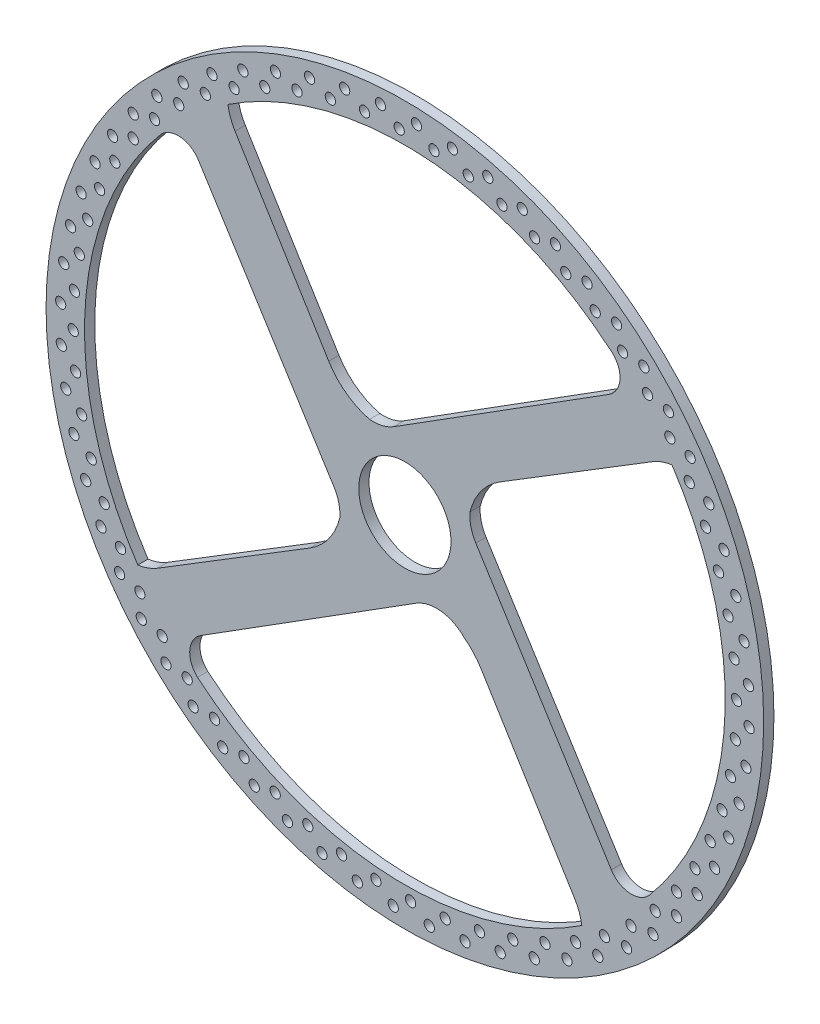
SolidWorks part; units mm, degrees
ref_plane "Front Plane" through (0, 0, 0) normal (0, 0, 1) x (1, 0, 0)
ref_plane "Top Plane" through (0, 0, 0) normal (0, 1, 0) x (1, 0, 0)
ref_plane "Right Plane" through (0, 0, 0) normal (1, 0, 0) x (0, 0, -1)
sketch "Sketch1" plane through (0, 0, 0) normal (0, 0, 1) x (1, 0, 0)
  line L3 (-2.1651, 13.8316) -> (39.8071, 40.2738)
  line L4 (18.5532, 14.856) -> (48.2752, 33.139)
  line L5 (14.856, -18.5532) -> (33.139, -48.2752)
  line L6 (13.8316, 2.1651) -> (40.2738, -39.8071)
  line L7 (-18.5532, -14.856) -> (-48.2752, -33.139)
  line L8 (2.1651, -13.8316) -> (-39.8071, -40.2738)
  line L9 (-14.856, 18.5532) -> (-33.139, 48.2752)
  line L10 (-13.8316, -2.1651) -> (-40.2738, 39.8071)
  circle A0 centre (0, 0) radius 14
  circle A1 centre (0, 0) radius 70
  arc A2 (40.4406, 47.653) -> (-34.5135, 52.1063) centre (0, 0) ccw
  arc A3 (39.8071, 40.2738) -> (40.4406, 47.653) centre (37.3316, 44.2031) ccw
  arc A4 (-2.1651, 13.8316) -> (-6.8889, 12.7065) centre (-6.178, 20.2013) cw
  arc A5 (48.2752, 33.139) -> (52.1063, 34.5135) centre (53.4637, 24.7041) cw
  arc A6 (18.5532, 14.856) -> (12.7065, 6.8889) centre (25.4254, 3.6841) ccw
  arc A7 (13.8316, 2.1651) -> (12.7065, 6.8889) centre (20.2013, 6.178) cw
  arc A8 (14.856, -18.5532) -> (11.5587, -14.9359) centre (3.6841, -25.4254) ccw
  arc A9 (33.139, -48.2752) -> (34.5135, -52.1063) centre (24.7041, -53.4637) cw
  arc A10 (40.2738, -39.8071) -> (47.653, -40.4406) centre (44.2031, -37.3316) ccw
  arc A11 (2.1651, -13.8316) -> (11.5587, -14.9359) centre (6.178, -20.2013) cw
  arc A12 (-18.5532, -14.856) -> (-12.7065, -6.8889) centre (-25.4254, -3.6841) ccw
  arc A13 (-48.2752, -33.139) -> (-52.1063, -34.5135) centre (-53.4637, -24.7041) cw
  arc A14 (-39.8071, -40.2738) -> (-40.4406, -47.653) centre (-37.3316, -44.2031) ccw
  arc A15 (-13.8316, -2.1651) -> (-12.7065, -6.8889) centre (-20.2013, -6.178) cw
  arc A16 (-14.856, 18.5532) -> (-6.8889, 12.7065) centre (-3.6841, 25.4254) ccw
  arc A17 (-33.139, 48.2752) -> (-34.5135, 52.1063) centre (-24.7041, 53.4637) cw
  arc A18 (-40.2738, 39.8071) -> (-47.653, 40.4406) centre (-44.2031, 37.3316) ccw
  arc A19 (-47.653, 40.4406) -> (-52.1063, -34.5135) centre (0, 0) ccw
  arc A20 (-40.4406, -47.653) -> (34.5135, -52.1063) centre (0, 0) ccw
  arc A21 (47.653, -40.4406) -> (52.1063, 34.5135) centre (0, 0) ccw
  point P59 (0, 0)
  dimension "D1" = 28
  dimension "D2" = 140
  dimension "D3" = 125
  dimension "D4" = 4
extrude "Boss-Extrude4" add sketch "Sketch1" along normal mid plane 2 contours A1 A18 A2 A17 A3 A5 A10 A9 A14 A13 | A18 L10 A15 A12 L7 A13 A2 A14 L8 A11 A8 L5 A9 A10 L6 A7 A6 L4 A5 A3 L3 A4 A16 L9 A17 A0
sketch "Sketch2" plane through (0, 0, 0) normal (0, 0, 1) x (1, 0, 0)
  circle A0 centre (0, 0) radius 9
  dimension "D1" = 18
extrude "Cut-Extrude3" cut sketch "Sketch2" against normal through all both and the other way through all
sketch "Sketch7" plane through (0, 0, 1) normal (0, 0, 1) x (1, 0, 0)
  circle A0 centre (41.3036, 52.9956) radius 1
  circle A1 centre (37.1313, 52.9956) radius 1
  dimension "D1" = 2
extrude "Cut-Extrude10" cut sketch "Sketch7" against normal blind 2
pattern_circular "CirPattern3" count 60 over 360 about axis through (0, 0, 0) along (0, 0, 1) of "Cut-Extrude10"
